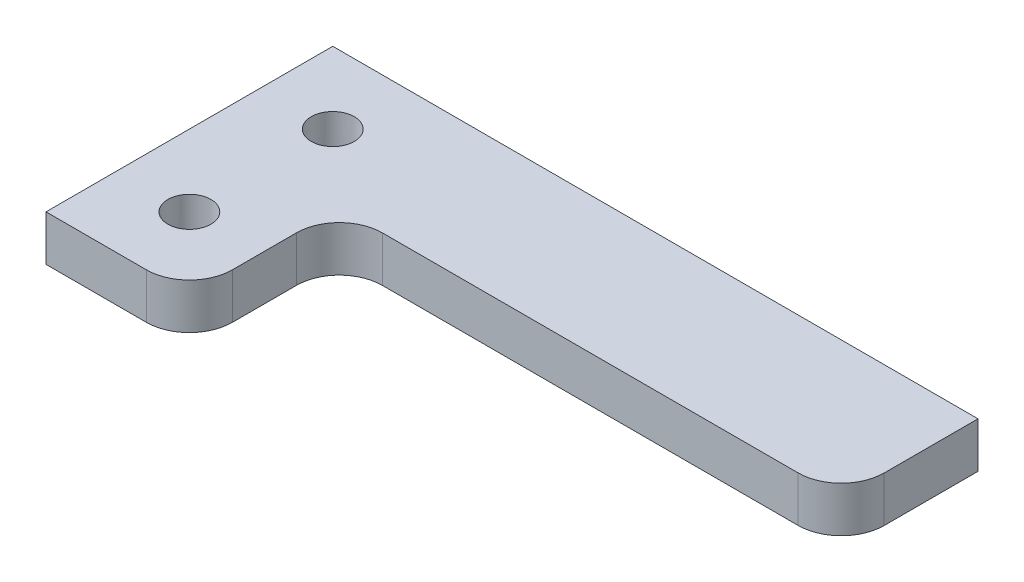
SolidWorks part; units mm, degrees
ref_plane "Front Plane" through (0, 0, 0) normal (0, 0, 1) x (1, 0, 0)
ref_plane "Top Plane" through (0, 0, 0) normal (0, 1, 0) x (1, 0, 0)
ref_plane "Right Plane" through (0, 0, 0) normal (1, 0, 0) x (0, 0, -1)
sketch "Sketch1" plane through (0, 0, 0) normal (0, 1, 0) x (1, 0, 0)
  line L0 (0, 0) -> (45, 0)
  line L1 (45, 0) -> (45, -6.5394)
  line L2 (42, -9.5394) -> (13, -9.5394)
  line L3 (0, -20) -> (7, -20)
  line L4 (0, -20) -> (0, 0)
  line L5 (10, -17) -> (10, -12.5394)
  arc A0 (10, -17) -> (7, -20) centre (7, -17) cw
  arc A1 (10, -12.5394) -> (13, -9.5394) centre (13, -12.5394) cw
  arc A2 (45, -6.5394) -> (42, -9.5394) centre (42, -6.5394) cw
  dimension "D5" = 3
  dimension "D1" = 45
  dimension "D2" = 20
  dimension "D3" = 10
  dimension "D4" = 10
extrude "Boss-Extrude1" add sketch "Sketch1" along normal blind 3.175
hole_wizard "Ø3.0 (3) Diameter Hole1" positions "Sketch3" profile "Sketch2" hole size "Ø3.0" standard "Ansi Metric"
sketch "Sketch3" plane through (0, 3.175, 0) normal (0, 1, 0) x (-1, 0, 0)
  line L0 (-5, 15) -> (-5, 5) construction
  line L2 (0, 0) -> (0, 20) construction
  line L3 (-45, 0) -> (0, 0) construction
  point P0 (-5, 5)
  point P1 (-5, 15)
  dimension "D1" = 5
  dimension "D2" = 5
  dimension "D3" = 10
sketch "Sketch2" plane through (5, 3.175, 5) normal (1, 0, 0) x (0, 0, 1)
  line L0 (0, 0) -> (0, 10.9013)
  line L1 (0, 10.9013) -> (1.5, 10)
  line L2 (1.5, 10) -> (1.5, 0)
  line L5 (1.5, 0) -> (0, 0)
  line L10 (0, 10.9013) -> (-1.5, 10) construction
  line L11 (0, -6.35) -> (0, 107.95) construction
  dimension "Hole Dia." = 3
  dimension "Hole Depth" = 10
  dimension "Drill Angle" = 118
